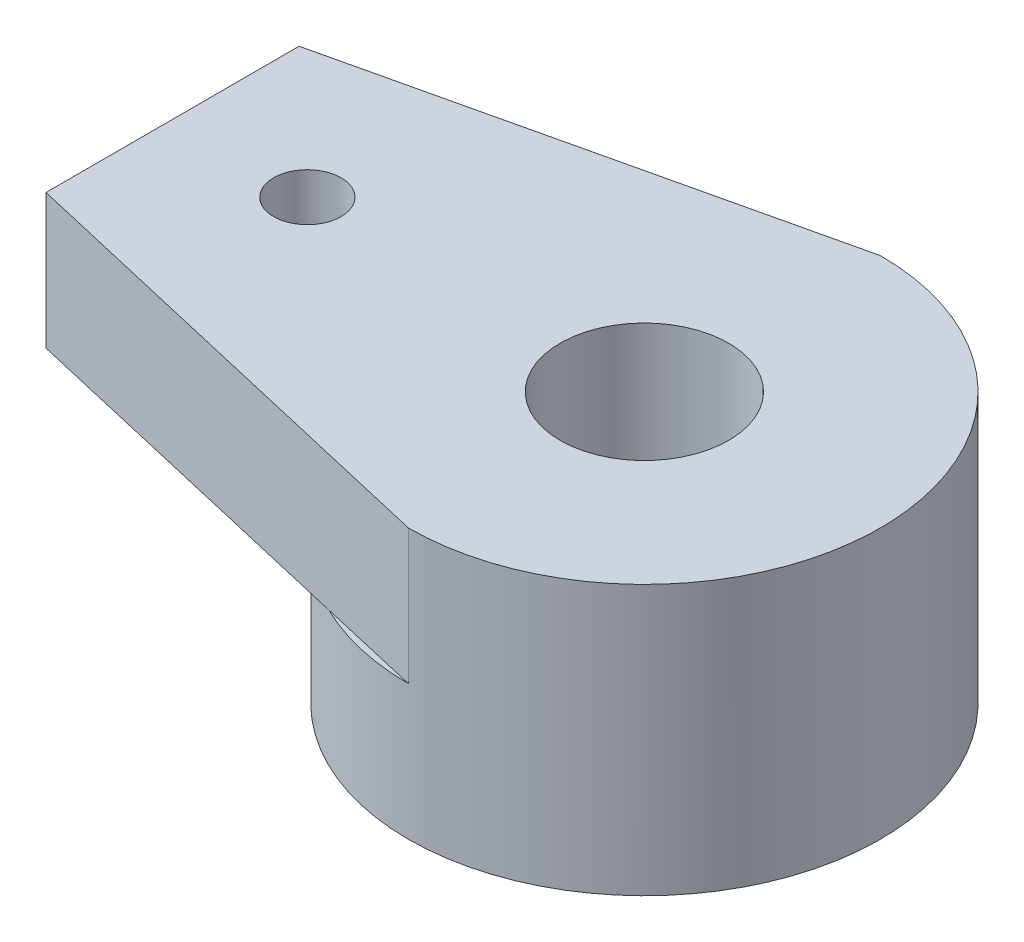
SolidWorks part; units mm, degrees
ref_plane "Front Plane" through (0, 0, 0) normal (0, 0, 1) x (1, 0, 0)
ref_plane "Top Plane" through (0, 0, 0) normal (0, 1, 0) x (1, 0, 0)
ref_plane "Right Plane" through (0, 0, 0) normal (1, 0, 0) x (0, 0, -1)
sketch "Sketch1" plane through (0, 0, 0) normal (0, 1, 0) x (1, 0, 0)
  circle A0 centre (0, 0) radius 3.5
  circle A1 centre (0, 0) radius 2.25
  dimension "D1" = 7
  dimension "D2" = 4.5
extrude "Boss-Extrude1" add sketch "Sketch1" along normal blind 2
sketch "Sketch2" plane through (0, 2, 0) normal (0, 1, 0) x (1, 0, 0)
  line L0 (0, 0) -> (-7, 0) construction
  line L1 (-7.0009, 1.878) -> (-6.9991, -1.878)
  line L4 (-7.0009, 1.878) -> (0, 3.5)
  line L5 (-6.9991, -1.878) -> (0, -3.5)
  circle A0 centre (0, 0) radius 1.25
  arc A1 (0, -3.5) -> (0, 3.5) centre (0, 0) ccw
  circle A8 centre (-5, 0) radius 0.5
  point P7 (-2.2388, -2.851)
  dimension "D1" = 3.5
  dimension "D2" = 2.5
  dimension "D3" = 5
  dimension "D6" = 7
extrude "Boss-Extrude3" add sketch "Sketch2" along normal blind 2
